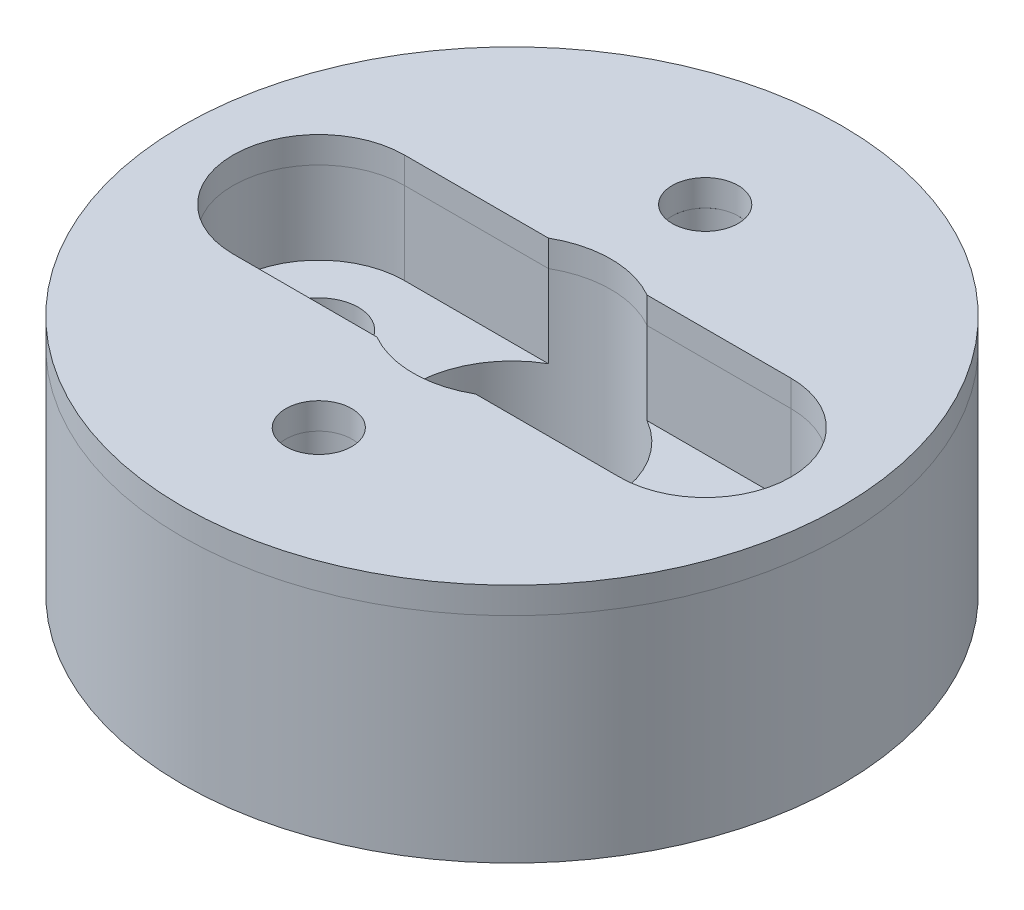
SolidWorks part; units mm, degrees
ref_plane "Front" through (0, 0, 0) normal (0, 0, 1) x (1, 0, 0)
ref_plane "Top" through (0, 0, 0) normal (0, 1, 0) x (1, 0, 0)
ref_plane "Right" through (0, 0, 0) normal (1, 0, 0) x (0, 0, -1)
sketch "Sketch1" plane through (0, 0, 0) normal (0, 1, 0) x (1, 0, 0)
  line L0 (0, 0) -> (7.4422, 0) construction
  line L1 (0, 0) -> (0, 2.3523) construction
  circle A1 centre (0, 0) radius 12.7
  circle A2 centre (7.4422, 0) radius 1.524
  circle A3 centre (-7.4422, 0) radius 1.524
  dimension "D2" = 25.4
  dimension "D3" = 3.048
  dimension "D1" = 7.4422
extrude "Boss-Extrude1" add sketch "Sketch1" along normal blind 8.255
sketch "Sketch2" plane through (0, 8.255, 0) normal (0, 1, 0) x (1, 0, 0)
  circle A0 centre (-7.4422, 0) radius 3.302
  circle A1 centre (7.4422, 0) radius 3.302
  dimension "D1" = 6.604
extrude "r" cut sketch "Sketch2" against normal blind 3.175
sketch "Sketch3" plane through (0, 8.255, 0) normal (0, 1, 0) x (1, 0, 0)
  line L0 (0, 0) -> (0, -7.4422) construction
  line L1 (0, 0) -> (1.0233, 0) construction
  circle A0 centre (0, -7.4422) radius 1.27
  circle A1 centre (0, 7.4422) radius 1.27
  dimension "D1" = 7.4422
  dimension "D2" = 2.54
extrude "Cut-Extrude2" cut sketch "Sketch3" against normal through all
sketch "Sketch4" plane through (0, 8.255, 0) normal (0, 1, 0) x (1, 0, 0)
  circle A0 centre (0, 0) radius 3.81
  dimension "D1" = 7.62
extrude "Cut-Extrude3" cut sketch "Sketch4" against normal through all
sketch "Sketch5" plane through (0, 8.255, 0) normal (0, 1, 0) x (1, 0, 0)
  line L0 (-7.4422, 0) -> (7.4422, 0) construction
  line L1 (-7.4422, 3.302) -> (7.4422, 3.302)
  line L2 (-7.4422, -3.302) -> (7.4422, -3.302)
  arc A0 (-7.4422, 3.302) -> (-7.4422, -3.302) centre (-7.4422, 0) ccw
  arc A1 (7.4422, -3.302) -> (7.4422, 3.302) centre (7.4422, 0) ccw
  circle A4 centre (7.4422, 0) radius 3.302 construction
  point P3 (0, 0)
extrude "Cut-Extrude4" cut sketch "Sketch5" against normal up to surface (3.175 mm away) up to face at (-7.4422, 5.08, 1.524)
sketch "Sketch6" plane through (0, 8.255, 0) normal (0, 1, 0) x (1, 0, 0)
  line L0 (-1.9008, 3.302) -> (-7.4422, 3.302) construction
  line L1 (-1.9008, 3.302) -> (-7.4422, 3.302)
  line L2 (7.4422, 3.302) -> (1.9008, 3.302) construction
  line L3 (1.9008, -3.302) -> (7.4422, -3.302) construction
  line L4 (-7.4422, -3.302) -> (-1.9008, -3.302) construction
  line L5 (7.4422, 3.302) -> (1.9008, 3.302)
  line L6 (1.9008, -3.302) -> (7.4422, -3.302)
  line L7 (-7.4422, -3.302) -> (-1.9008, -3.302)
  circle A0 centre (0, -7.4422) radius 1.27 construction
  circle A1 centre (0, 0) radius 12.7
  circle A2 centre (0, 0) radius 12.7
  circle A3 centre (0, 7.4422) radius 1.27 construction
  circle A4 centre (0, -7.4422) radius 1.27
  circle A5 centre (0, 7.4422) radius 1.27
  arc A6 (1.9008, 3.302) -> (-1.9008, 3.302) centre (0, 0) ccw construction
  arc A7 (7.4422, -3.302) -> (7.4422, 3.302) centre (7.4422, 0) ccw construction
  arc A8 (-1.9008, -3.302) -> (1.9008, -3.302) centre (0, 0) ccw construction
  arc A9 (-7.4422, 3.302) -> (-7.4422, -3.302) centre (-7.4422, 0) ccw construction
  arc A10 (1.9008, 3.302) -> (-1.9008, 3.302) centre (0, 0) ccw
  arc A11 (7.4422, -3.302) -> (7.4422, 3.302) centre (7.4422, 0) ccw
  arc A12 (-1.9008, -3.302) -> (1.9008, -3.302) centre (0, 0) ccw
  arc A13 (-7.4422, 3.302) -> (-7.4422, -3.302) centre (-7.4422, 0) ccw
  dimension "D1" = 0
extrude "Extra_Height" add sketch "Sketch6" along normal blind 1.016 separate body
equation "\"Spacing\"= 0.293"
equation "\"D1@Sketch1\"=\"Spacing\""
equation "\"D1@Sketch3\"=\"Spacing\""
